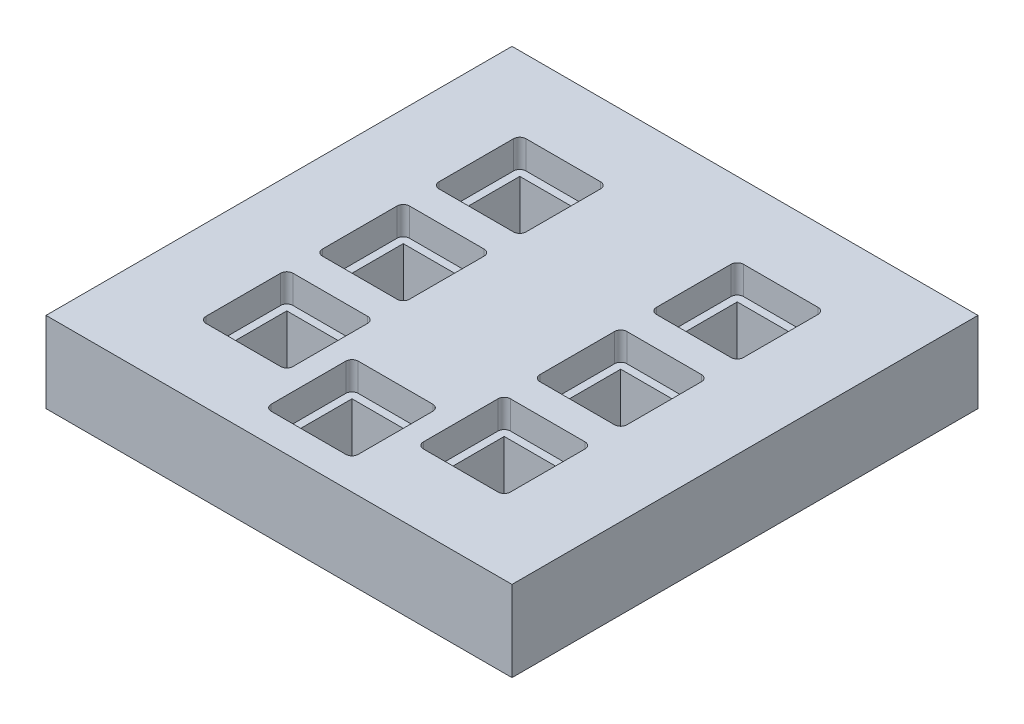
SolidWorks part; units mm, degrees
ref_plane "Front Plane" through (0, 0, 0) normal (0, 0, 1) x (1, 0, 0)
ref_plane "Top Plane" through (0, 0, 0) normal (0, 1, 0) x (1, 0, 0)
ref_plane "Right Plane" through (0, 0, 0) normal (1, 0, 0) x (0, 0, -1)
sketch "Sketch1" plane through (0, 0, 0) normal (0, 1, 0) x (1, 0, 0)
  line L0 (0, 0) -> (0, 50000) construction
  line L1 (75, -75) -> (-75, -75)
  line L2 (75, -75) -> (75, 75)
  line L3 (75, 75) -> (-75, 75)
  line L4 (-75, -75) -> (-75, 75)
  line L5 (75, -75) -> (-75, 75) construction
  line L6 (75, 75) -> (-75, -75) construction
  line L7 (0, 0) -> (-50000, 0) construction
  point P0 (0, 0)
  dimension "D1" = 150
  dimension "D2" = 150
extrude "Boss-Extrude1" add sketch "Sketch1" along normal blind 26
sketch "Sketch2" plane through (0, 26, 0) normal (0, 1, 0) x (1, 0, 0)
  line L1 (0, 0) -> (-50000, 0) construction
  line L2 (-35, 78.1261) -> (-35, 50078.1261) construction
  line L4 (-47, 23.5) -> (-23, 23.5)
  line L5 (-47, 14) -> (-23, 14)
  line L6 (-49, 12) -> (-49, -12)
  line L7 (-47, -14) -> (-23, -14)
  line L8 (-21, 12) -> (-21, -12)
  line L9 (-47, 51.5) -> (-23, 51.5)
  line L10 (-49, 49.5) -> (-49, 25.5)
  line L11 (-21, 49.5) -> (-21, 25.5)
  line L12 (-21, -49.5) -> (-21, -25.5)
  line L13 (-49, -49.5) -> (-49, -25.5)
  line L14 (-47, -51.5) -> (-23, -51.5)
  line L15 (-47, -23.5) -> (-23, -23.5)
  line L16 (47, -23.5) -> (23, -23.5)
  line L17 (47, -51.5) -> (23, -51.5)
  line L18 (49, -49.5) -> (49, -25.5)
  line L19 (21, -49.5) -> (21, -25.5)
  line L20 (21, 49.5) -> (21, 25.5)
  line L21 (49, 49.5) -> (49, 25.5)
  line L22 (47, 51.5) -> (23, 51.5)
  line L23 (21, 12) -> (21, -12)
  line L24 (47, -14) -> (23, -14)
  line L25 (49, 12) -> (49, -12)
  line L26 (47, 14) -> (23, 14)
  line L27 (47, 23.5) -> (23, 23.5)
  line L28 (0, -51.5) -> (-50000, -51.5) construction
  line L29 (-12, -37.5) -> (12, -37.5)
  line L30 (-14, -39.5) -> (-14, -63.5)
  line L31 (-12, -65.5) -> (12, -65.5)
  line L32 (14, -39.5) -> (14, -63.5)
  line L33 (-75, -75) -> (75, -75) construction
  arc A0 (-49, -12) -> (-47, -14) centre (-47, -12) ccw
  arc A1 (-23, -14) -> (-21, -12) centre (-23, -12) ccw
  arc A2 (-23, 14) -> (-21, 12) centre (-23, 12) cw
  arc A3 (-47, 14) -> (-49, 12) centre (-47, 12) ccw
  arc A4 (-49, 25.5) -> (-47, 23.5) centre (-47, 25.5) ccw
  arc A5 (-23, 23.5) -> (-21, 25.5) centre (-23, 25.5) ccw
  arc A6 (-47, 51.5) -> (-49, 49.5) centre (-47, 49.5) ccw
  arc A7 (-23, 51.5) -> (-21, 49.5) centre (-23, 49.5) cw
  arc A8 (-23, -51.5) -> (-21, -49.5) centre (-23, -49.5) ccw
  arc A9 (-47, -51.5) -> (-49, -49.5) centre (-47, -49.5) cw
  arc A10 (-23, -23.5) -> (-21, -25.5) centre (-23, -25.5) cw
  arc A11 (-49, -25.5) -> (-47, -23.5) centre (-47, -25.5) cw
  arc A12 (49, -25.5) -> (47, -23.5) centre (47, -25.5) ccw
  arc A13 (23, -23.5) -> (21, -25.5) centre (23, -25.5) ccw
  arc A14 (47, -51.5) -> (49, -49.5) centre (47, -49.5) ccw
  arc A15 (23, -51.5) -> (21, -49.5) centre (23, -49.5) cw
  arc A16 (23, 51.5) -> (21, 49.5) centre (23, 49.5) ccw
  arc A17 (47, 51.5) -> (49, 49.5) centre (47, 49.5) cw
  arc A18 (23, 23.5) -> (21, 25.5) centre (23, 25.5) cw
  arc A19 (49, 25.5) -> (47, 23.5) centre (47, 25.5) cw
  arc A20 (47, 14) -> (49, 12) centre (47, 12) cw
  arc A21 (23, 14) -> (21, 12) centre (23, 12) ccw
  arc A22 (23, -14) -> (21, -12) centre (23, -12) cw
  arc A23 (49, -12) -> (47, -14) centre (47, -12) cw
  arc A24 (-14, -63.5) -> (-12, -65.5) centre (-12, -63.5) ccw
  arc A25 (12, -65.5) -> (14, -63.5) centre (12, -63.5) ccw
  arc A26 (12, -37.5) -> (14, -39.5) centre (12, -39.5) cw
  arc A27 (-12, -37.5) -> (-14, -39.5) centre (-12, -39.5) ccw
  point P13 (-35, 14)
  point P14 (-49, 0)
  point P17 (-49, -14)
  point P22 (-21, 14)
  point P25 (-49, 14)
  point P30 (-35, 53.1521)
  point P41 (-35, 23.5)
  point P90 (49, 14)
  point P91 (21, 14)
  point P92 (49, -14)
  point P102 (-14, -51.5)
  point P105 (-14, -65.5)
  point P110 (14, -37.5)
  point P113 (-14, -37.5)
  dimension "D5" = 2
  dimension "D6" = 2
  dimension "D12" = 2
  dimension "D3" = 28
  dimension "D4" = 28
  dimension "D7" = 28
  dimension "D8" = 28
  dimension "D9" = 28
  dimension "D10" = 28
  dimension "D11" = 23.5
extrude "Cut-Extrude1" cut sketch "Sketch2" against normal blind 9
sketch "Sketch3" plane through (0, 17, 0) normal (0, 1, 0) x (1, 0, 0)
  line L1 (0, 0) -> (-50000, 0) construction
  line L2 (-35, 23.5) -> (-35, 50023.5) construction
  line L3 (-47, 23.5) -> (-23, 23.5) construction
  line L6 (-23.5, -37.5) -> (-50023.5, -37.5) construction
  line L7 (-21, -49.5) -> (-21, -25.5) construction
  line L8 (-23.5, -49) -> (-23.5, -26)
  line L9 (-46.5, 49) -> (-23.5, 49)
  line L10 (-46.5, 49) -> (-46.5, 26)
  line L11 (-46.5, 26) -> (-23.5, 26)
  line L12 (-23.5, 49) -> (-23.5, 26)
  line L13 (-46.5, -26) -> (-23.5, -26)
  line L14 (-46.5, -49) -> (-46.5, -26)
  line L15 (-46.5, -49) -> (-23.5, -49)
  line L16 (46.5, -49) -> (23.5, -49)
  line L17 (46.5, -49) -> (46.5, -26)
  line L18 (46.5, -26) -> (23.5, -26)
  line L19 (23.5, 49) -> (23.5, 26)
  line L20 (46.5, 26) -> (23.5, 26)
  line L21 (46.5, 49) -> (46.5, 26)
  line L22 (46.5, 49) -> (23.5, 49)
  line L23 (23.5, -49) -> (23.5, -26)
  line L24 (-46.5, 11.5) -> (-23.5, 11.5)
  line L25 (-46.5, -11.5) -> (-23.5, -11.5)
  line L26 (-46.5, 11.5) -> (-46.5, -11.5)
  line L27 (-23.5, 11.5) -> (-23.5, -11.5)
  line L28 (23.5, 11.5) -> (23.5, -11.5)
  line L29 (46.5, 11.5) -> (46.5, -11.5)
  line L30 (46.5, -11.5) -> (23.5, -11.5)
  line L31 (46.5, 11.5) -> (23.5, 11.5)
  line L32 (-14, -51.5) -> (-50014, -51.5) construction
  line L33 (-11.5, -40) -> (11.5, -40)
  line L34 (-11.5, -40) -> (-11.5, -63)
  line L35 (-11.5, -63) -> (11.5, -63)
  line L36 (11.5, -40) -> (11.5, -63)
  line L37 (-14, -39.5) -> (-14, -63.5) construction
  point P9 (-35, 23.5)
  point P19 (-21, -37.5)
  point P24 (-35, 49)
  point P43 (-49, 0)
  point P44 (-23.5, 0)
  point P45 (-35, 11.5)
  point P46 (-35, -11.5)
  point P59 (-14, -51.5)
  point P60 (-11.5, -51.5)
  dimension "D1" = 23
  dimension "D3" = 23
  dimension "D4" = 23
  dimension "D5" = 23
  dimension "D6" = 23
extrude "Cut-Extrude2" cut sketch "Sketch3" against normal through all
